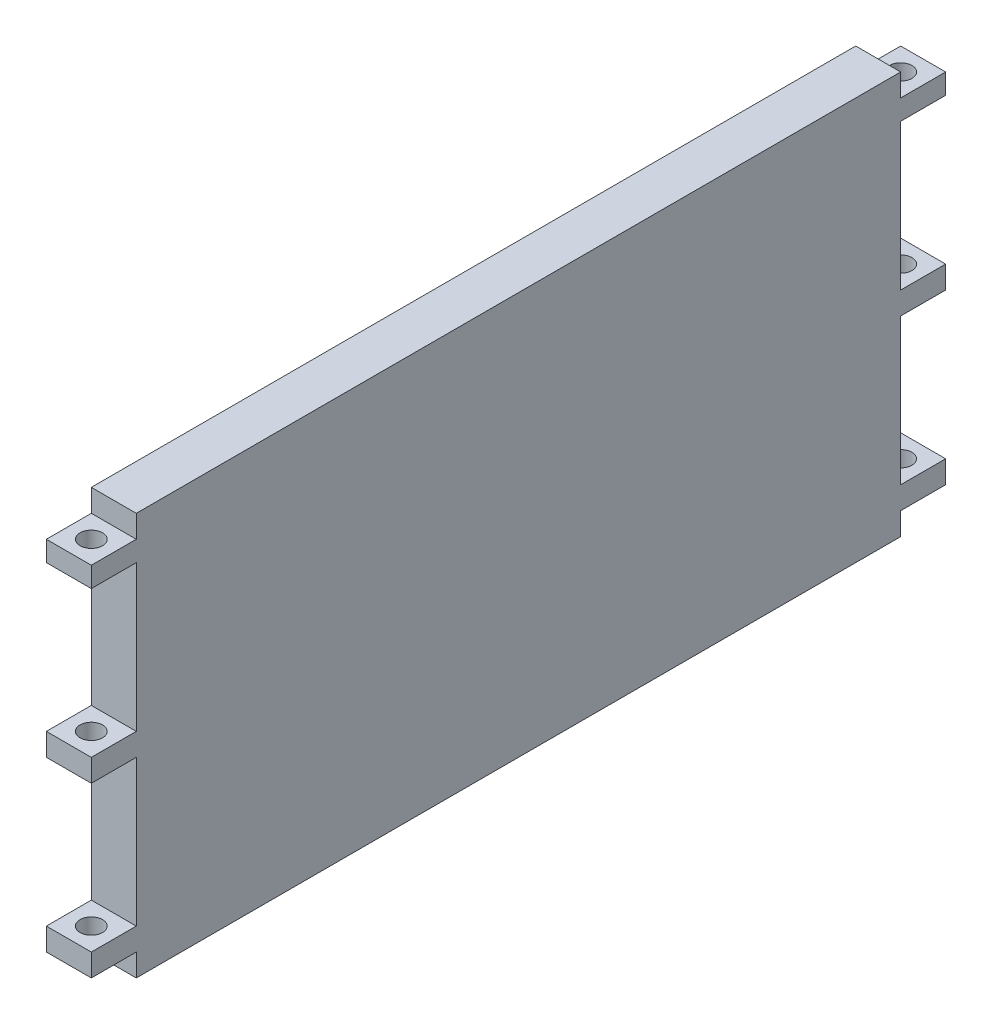
SolidWorks part; units mm, degrees
ref_plane "Front Plane" through (0, 0, 0) normal (0, 0, 1) x (1, 0, 0)
ref_plane "Top Plane" through (0, 0, 0) normal (0, 1, 0) x (1, 0, 0)
ref_plane "Right Plane" through (0, 0, 0) normal (1, 0, 0) x (0, 0, -1)
sketch "Sketch1" plane through (0, 0, 0) normal (1, 0, 0) x (0, 0, -1)
  line L1 (-190, 89.5) -> (190, 89.5)
  line L2 (-190, 89.5) -> (-190, -89.5)
  line L3 (-190, -89.5) -> (190, -89.5)
  line L4 (190, 89.5) -> (190, -89.5)
  line L5 (-190, 89.5) -> (190, -89.5) construction
  line L6 (-190, -89.5) -> (190, 89.5) construction
  point P0 (0, 0)
  dimension "D1" = 380
  dimension "D2" = 179
extrude "Boss-Extrude1" add sketch "Sketch1" along normal blind 20
sketch "Sketch2" plane through (0, 0, 190) normal (0, 0, 1) x (1, 0, 0)
  line L0 (0, 89.5) -> (0, -89.5) construction
  line L1 (0, 70.5) -> (20, 70.5)
  line L2 (0, 70.5) -> (0, 5.5)
  line L3 (0, 5.5) -> (20, 5.5)
  line L4 (20, 70.5) -> (20, 5.5)
  line L5 (20, 89.5) -> (20, -89.5) construction
  line L6 (20, 89.5) -> (0, 89.5) construction
  line L8 (0, 89.5) -> (20, 89.5)
  line L9 (0, 89.5) -> (0, 79.5)
  line L10 (0, 79.5) -> (20, 79.5)
  line L11 (20, 89.5) -> (20, 79.5)
  line L12 (0, -89.5) -> (20, -89.5)
  line L13 (0, -89.5) -> (0, -79.5)
  line L14 (0, -79.5) -> (20, -79.5)
  line L15 (20, -89.5) -> (20, -79.5)
  line L16 (0, -4.5) -> (20, -4.5)
  line L17 (0, -4.5) -> (0, -69.5)
  line L18 (0, -69.5) -> (20, -69.5)
  line L19 (20, -4.5) -> (20, -69.5)
  dimension "D1" = 65
  dimension "D2" = 19
  dimension "D3" = 10
  dimension "D4" = 10
  dimension "D5" = 65
  dimension "D6" = 10
extrude "Cut-Extrude1" cut sketch "Sketch2" against normal blind 20
sketch "Sketch3" plane through (0, 79.5, 0) normal (0, 1, 0) x (1, 0, 0)
  line L0 (0, -170) -> (0, -190) construction
  line L1 (0, -190) -> (20, -190) construction
  circle A0 centre (10, -180) radius 5
  dimension "D1" = 10
  dimension "D2" = 10
  dimension "D3" = 10
extrude "Cut-Extrude2" cut sketch "Sketch3" against normal up to surface (159 mm away) up to face at (10, -79.5, 180)
mirror "Mirror2" about plane through (0, 0, 0) normal (0, 0, 1) of "Cut-Extrude2", "Cut-Extrude1"
